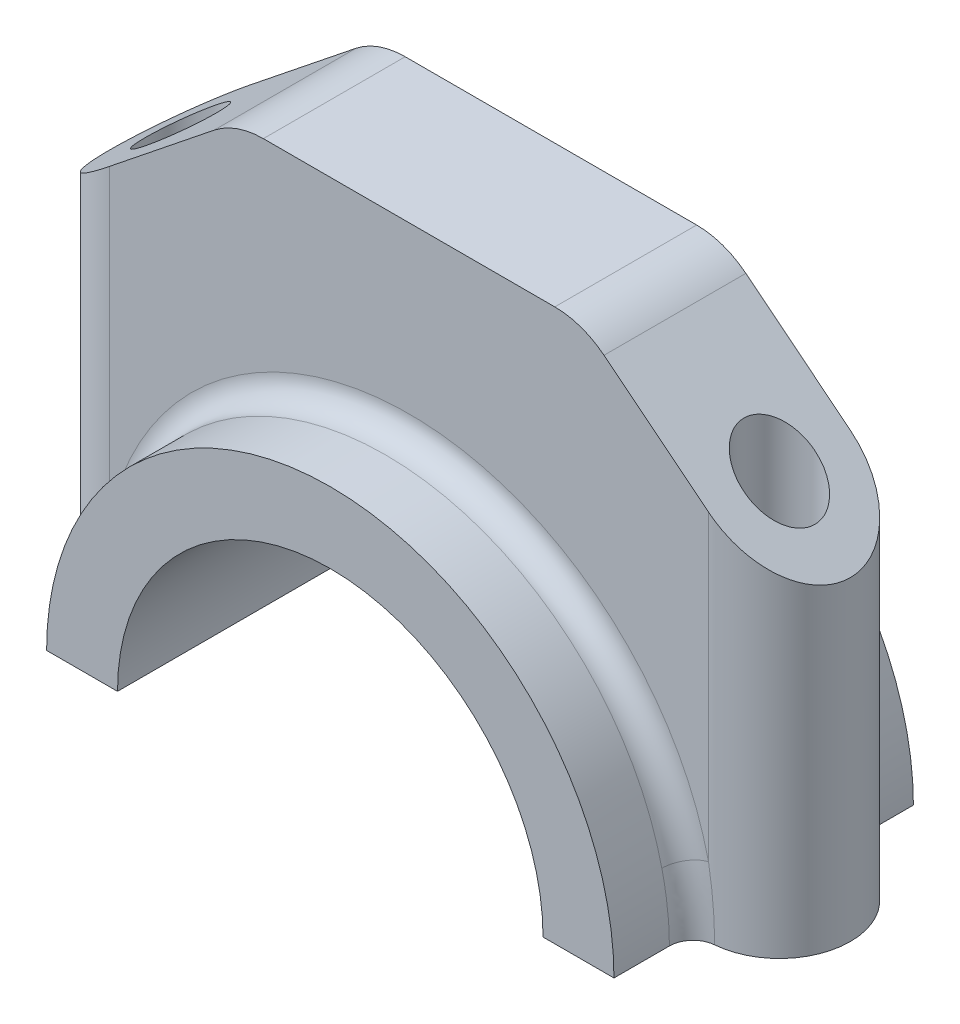
SolidWorks part; units mm, degrees
ref_plane "Front Plane" through (0, 0, 0) normal (0, 0, 1) x (1, 0, 0)
ref_plane "Top Plane" through (0, 0, 0) normal (0, 1, 0) x (1, 0, 0)
ref_plane "Right Plane" through (0, 0, 0) normal (1, 0, 0) x (0, 0, -1)
sketch "Sketch1" plane through (0, 0, 0) normal (0, 0, 1) x (1, 0, 0)
  line L0 (-36, 0) -> (-27, 0)
  line L1 (27, 0) -> (36, 0)
  arc A0 (36, 0) -> (-36, 0) centre (0, 0) ccw
  arc A1 (27, 0) -> (-27, 0) centre (0, 0) ccw
  dimension "D1" = 54
  dimension "D2" = 72
extrude "Boss-Extrude1" add sketch "Sketch1" along normal mid plane 38
ref_plane "Plane1" through (0, 60, 0) normal (0, -1, 0) x (-1, 0, 0)
sketch "Sketch2" plane through (0, 60, 0) normal (0, -1, 0) x (-1, 0, 0)
  line L0 (38, 0) -> (-38, 0) construction
  line L1 (38, -9) -> (-38, -9)
  line L2 (38, 9) -> (-38, 9)
  arc A0 (38, -9) -> (38, 9) centre (38, 0) ccw
  arc A1 (-38, 9) -> (-38, -9) centre (-38, 0) ccw
  point P2 (0, 0)
  dimension "D2" = 9
  dimension "D1" = 76
extrude "Boss-Extrude2" add sketch "Sketch2" along normal up to surface (60 mm away) up to face at (-31.5, 0, 0)
sketch "Sketch3" plane through (0, 0, 9) normal (0, 0, 1) x (1, 0, 0)
  line L1 (-27, 0) -> (27, 0)
  line L2 (-27, 0) -> (27, 0)
  arc A1 (27, 0) -> (-27, 0) centre (0, 0) ccw
  arc A2 (27, 0) -> (-27, 0) centre (0, 0) ccw
  dimension "D1" = 0
extrude "Cut-Extrude1" cut sketch "Sketch3" against normal through all
sketch "Sketch4" plane through (0, 0, 0) normal (0, -1, 0) x (1, 0, 0)
  circle A0 centre (-38, 0) radius 4.5
  circle A1 centre (38, 0) radius 4.5
  dimension "D1" = 9
  dimension "D2" = 9
extrude "Cut-Extrude2" cut sketch "Sketch4" against normal through all
sketch "Sketch5" plane through (0, 0, 0) normal (0, 0, 1) x (1, 0, 0)
  line L4 (-47, 40) -> (-22, 60)
  line L5 (-47, 60) -> (-47, 0) construction
  line L7 (38, 60) -> (-38, 60) construction
  line L8 (-22, 60) -> (-47, 60)
  line L9 (-47, 60) -> (-47, 40)
  line L10 (0, 0) -> (0, 27) construction
  line L11 (47, 60) -> (47, 40)
  line L12 (22, 60) -> (47, 60)
  line L13 (47, 40) -> (22, 60)
  arc A0 (27, 0) -> (-27, 0) centre (0, 0) ccw construction
  dimension "D1" = 20
  dimension "D2" = 25
extrude "Cut-Extrude4" cut sketch "Sketch5" against normal through all both and the other way through all
fillet "Fillet1" radius 10 2 edges at (-22, 60, 0) (22, 60, 0)
fillet "Fillet2" radius 3 2 edges at (0, 36, 9) (0, 36, -9)
